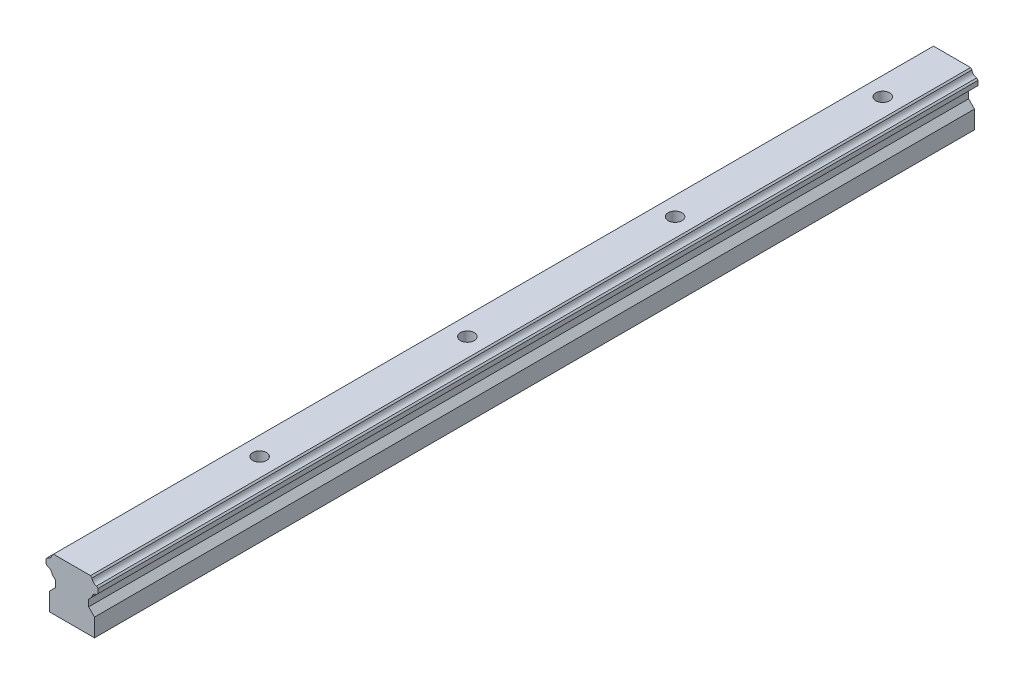
SolidWorks part; units mm, degrees
ref_plane "Front Plane" through (0, 0, 0) normal (0, 0, 1) x (1, 0, 0)
ref_plane "Top Plane" through (0, 0, 0) normal (0, 1, 0) x (1, 0, 0)
ref_plane "Right Plane" through (0, 0, 0) normal (1, 0, 0) x (0, 0, -1)
sketch "Sketch1" plane through (0, 0, 0) normal (0, 0, 1) x (1, 0, 0)
  line B0 (-6.5, 0) -> (6.5, 0)
  line B1 (-6.5, 5.2) -> (-6.5, 0)
  line B2 (6.5, 5.2) -> (6.5, 0)
  line B3 (-6.5, 5.2) -> (-4.8, 6.9)
  line B4 (-4.8, 6.9) -> (-4.8, 8.84)
  line B5 (-4.8, 8.84) -> (-5.7549, 9.7949)
  line B6 (-7.0851, 11.1251) -> (-7.5, 11.54)
  line B7 (-7.5, 11.54) -> (-7.5, 12.85)
  line B8 (-7.5, 12.85) -> (-7.0816, 13.2684)
  line B9 (-5.7554, 14.5946) -> (-5.35, 15)
  line B10 (-5.35, 15) -> (5.35, 15)
  line B11 (5.35, 15) -> (5.7554, 14.5946)
  line B12 (7.0816, 13.2684) -> (7.5, 12.85)
  line B13 (7.5, 12.85) -> (7.5, 11.54)
  line B14 (7.5, 11.54) -> (7.0851, 11.1251)
  line B15 (5.7549, 9.7949) -> (4.8, 8.84)
  line B16 (4.8, 8.84) -> (4.8, 6.9)
  line B17 (4.8, 6.9) -> (6.5, 5.2)
  line B18 (9.5, 5.2) -> (9.5, 16) construction
  arc B19 (-5.7549, 9.7949) -> (-7.0851, 11.1251) centre (-7.3, 9.58) ccw
  arc B20 (-7.0816, 13.2684) -> (-5.7554, 14.5946) centre (-7.3, 14.813) ccw
  arc B21 (5.7554, 14.5946) -> (7.0816, 13.2684) centre (7.3, 14.813) ccw
  arc B22 (7.0851, 11.1251) -> (5.7549, 9.7949) centre (7.3, 9.58) ccw
sketch_block_instance "Block-RailTopography-1"
sketch_block "Block-RailTopography" parameters "D1"=15
extrude "Boss-Extrude1" add sketch "Sketch1" along normal blind 254
sketch "Sketch2" plane through (0, 15, 0) normal (0, 1, 0) x (1, 0, 0)
  line L0 (0, -1000) -> (0, 49000) construction
  circle A0 centre (0, -20) radius 2
  circle A1 centre (0, -79.944) radius 2
  circle A2 centre (0, -139.888) radius 2
  circle A3 centre (0, -199.832) radius 2
  dimension "D2" = 4
  dimension "D1" = 20
  dimension "D3" = 4
extrude "Cut-Extrude1" cut sketch "Sketch2" against normal through all
